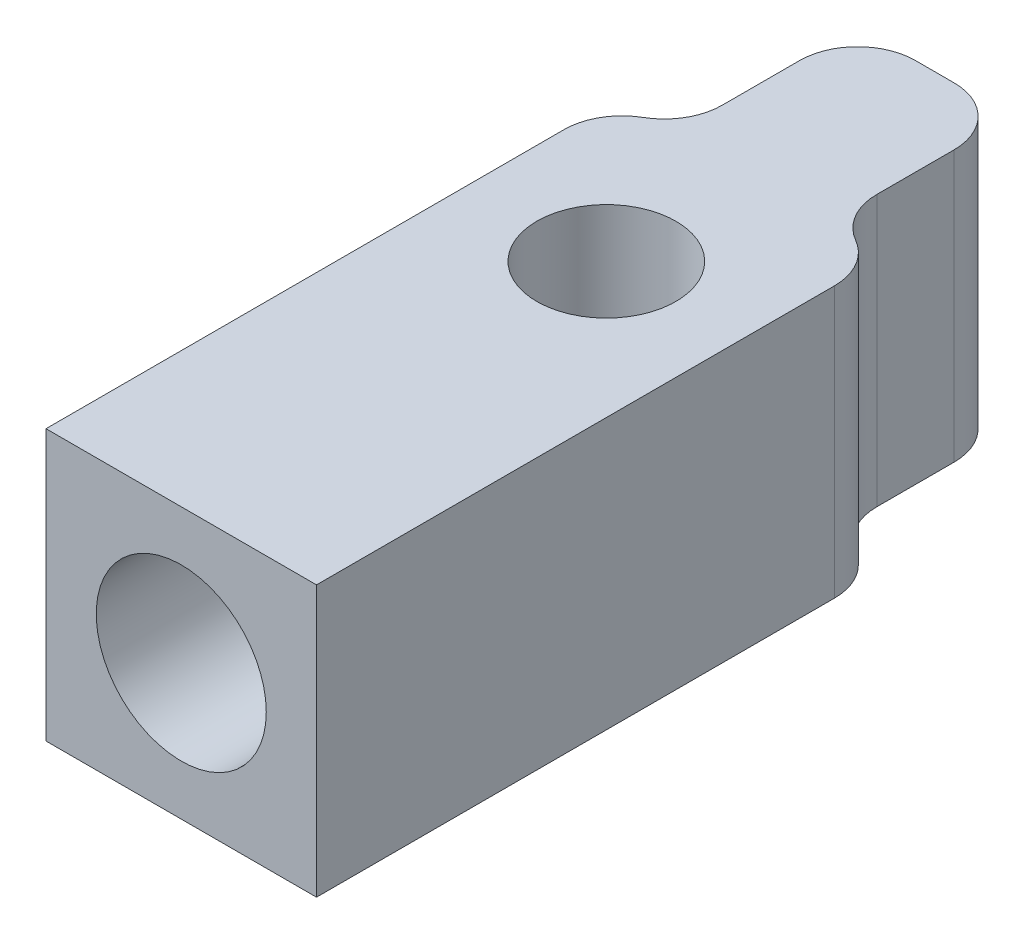
SolidWorks part; units mm, degrees
ref_plane "Front Plane" through (0, 0, 0) normal (0, 0, 1) x (1, 0, 0)
ref_plane "Top Plane" through (0, 0, 0) normal (0, 1, 0) x (1, 0, 0)
ref_plane "Right Plane" through (0, 0, 0) normal (1, 0, 0) x (0, 0, -1)
ref_plane "Plane1" through (-3.5, 0, 0) normal (-1, 0, 0) x (0, -1, 0)
sketch "Sketch1" plane through (-3.5, 0, 0) normal (-1, 0, 0) x (0, -1, 0)
  line L0 (-1.5, -8.5) -> (-1.5, 11)
  line L1 (-1.5, 11) -> (-8.5, 11)
  line L2 (-8.5, 11) -> (-8.5, -8.5)
  line L3 (-8.5, -8.5) -> (-1.5, -8.5)
extrude "Boss-Extrude1" add sketch "Sketch1" against normal blind 7
sketch "Sketch2" plane through (0, 8.5, 0) normal (0, 1, 0) x (-1, 0, 0)
  line L0 (-3.5, -2.4019) -> (-3.5, -8.5)
  line L1 (-3.5, -8.5) -> (-2, -8.5)
  line L2 (-2, -8.5) -> (-2, -5)
  arc A0 (-2.75, -3.701) -> (-3.5, -2.4019) centre (-2, -2.4019) cw
  arc A1 (-2, -5) -> (-2.75, -3.701) centre (-3.5, -5) ccw
extrude "Cut-Extrude1" cut sketch "Sketch2" against normal through all
sketch "Sketch3" plane through (0, 8.5, 0) normal (0, 1, 0) x (-1, 0, 0)
  line L0 (2, -5) -> (2, -8.5)
  line L1 (2, -8.5) -> (3.5, -8.5)
  line L2 (3.5, -8.5) -> (3.5, -2.4019)
  arc A0 (3.5, -2.4019) -> (2.75, -3.701) centre (2, -2.4019) cw
  arc A1 (2.75, -3.701) -> (2, -5) centre (3.5, -5) ccw
extrude "Cut-Extrude2" cut sketch "Sketch3" against normal through all
fillet "Fillet1" radius 1.5 2 edges at (-2, 5, -8.5) (2, 5, -8.5)
sketch "Sketch4" plane through (0, 8.5, 0) normal (0, 1, 0) x (1, 0, 0)
  line L0 (0.5, 8.5) -> (-0.5, 8.5) construction
  circle A0 centre (0, 0) radius 1.8
  dimension "D1" = 3.6
  dimension "D2" = 8.5
extrude "Cut-Extrude3" cut sketch "Sketch4" against normal up to next
sketch "Sketch5" plane through (0, 0, 11) normal (0, 0, 1) x (1, 0, 0)
  line L0 (3.5, 8.5) -> (-3.5, 8.5) construction
  line L1 (-3.5, 1.5) -> (-3.5, 8.5) construction
  circle A0 centre (0, 5) radius 2.2
  point P4 (0, 8.5)
  point P7 (-3.5, 5)
  dimension "D1" = 4.4
  dimension "D2" = 0
  dimension "D3" = 0
extrude "Cut-Extrude4" cut sketch "Sketch5" against normal blind 7
